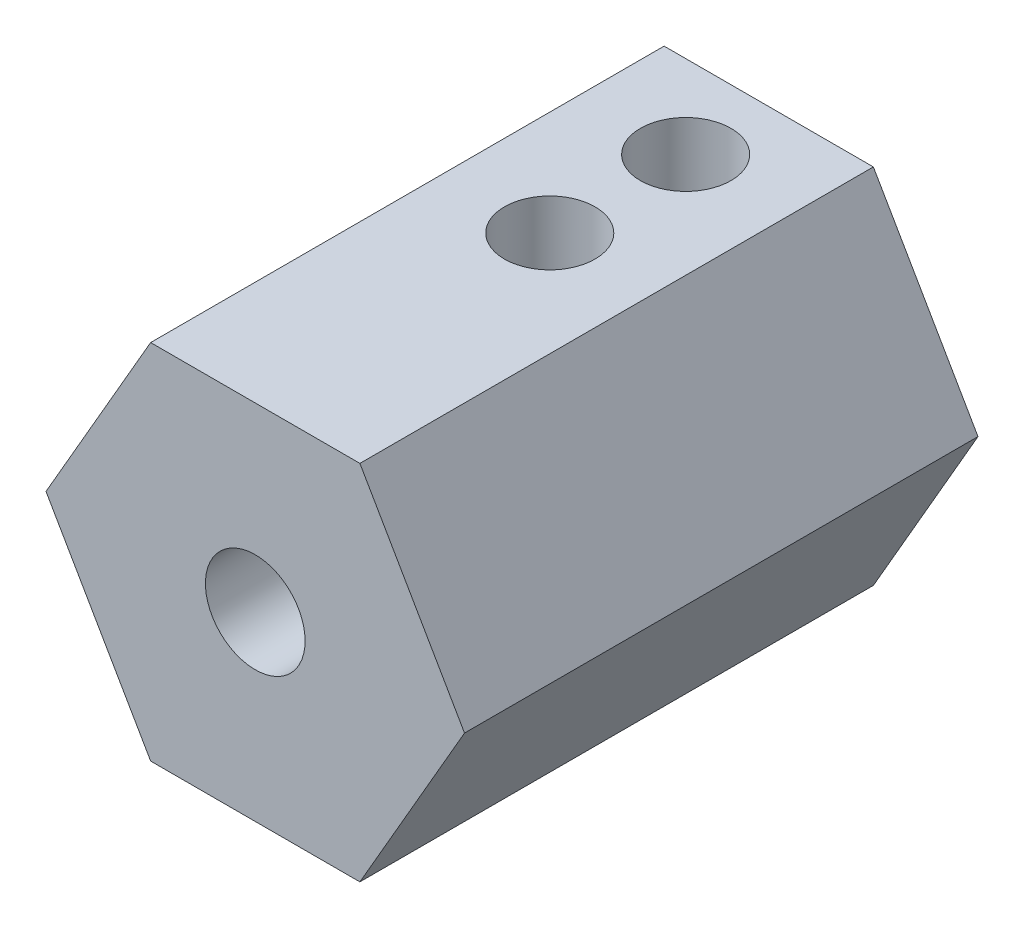
SolidWorks part; units mm, degrees
material "6061-T6 (SS)"
ref_plane "Front Plane" through (0, 0, 0) normal (0, 0, 1) x (1, 0, 0)
ref_plane "Top Plane" through (0, 0, 0) normal (0, 1, 0) x (1, 0, 0)
ref_plane "Right Plane" through (0, 0, 0) normal (1, 0, 0) x (0, 0, -1)
sketch "Sketch1" plane through (0, 0, 0) normal (0, 0, 1) x (1, 0, 0)
  line L1 (3.4641, 6) -> (-3.4641, 6)
  line L2 (-3.4641, 6) -> (-6.9282, 0)
  line L3 (-6.9282, 0) -> (-3.4641, -6)
  line L4 (-3.4641, -6) -> (3.4641, -6)
  line L5 (3.4641, -6) -> (6.9282, 0)
  line L6 (6.9282, 0) -> (3.4641, 6)
  circle A0 centre (0, 0) radius 6 construction
  dimension "D1" = 12
extrude "Boss-Extrude1" add sketch "Sketch1" along normal mid plane 17
ref_plane "Plane1" through (0, 0, 1.5) normal (0, 0, 1) x (1, 0, 0)
sketch "Sketch2" plane through (0, 0, -8.5) normal (0, 0, -1) x (-1, 0, 0)
  circle A0 centre (0, 0) radius 2
  dimension "D1" = 4
extrude "Cut-Extrude1" cut sketch "Sketch2" against normal up to surface (10 mm away)
hole_wizard "M4x0.7 Tapped Hole1" positions "Sketch6" profile "Sketch8" tap size "M4x0.7" standard "ANSI Metric"
sketch "Sketch6" plane through (0, 0, 8.5) normal (0, 0, 1) x (1, 0, 0)
  point P0 (0, 0)
sketch "Sketch8" plane through (0, 0, 8.5) normal (1, 0, 0) x (0, -1, 0)
  line L0 (0, 0) -> (0, 7.9914)
  line L1 (0, 7.9914) -> (1.65, 7)
  line L2 (1.65, 7) -> (1.65, 0)
  line L5 (1.65, 0) -> (0, 0)
  line L10 (0, 7.9914) -> (-1.65, 7) construction
  line L11 (0, -6.35) -> (0, 107.95) construction
  dimension "Tap Drill Dia." = 3.3
  dimension "Tap Drill Depth" = 7
  dimension "Drill Angle" = 118
cosmetic thread "Hole Thread1" parameters "D1"=8, "D2"=4
hole_wizard "M3x0.5 Tapped Hole1" positions "Sketch4" profile "Sketch5" tap size "M3x0.5" standard "ANSI Metric"
sketch "Sketch4" plane through (0, 6, 0) normal (0, 1, 0) x (1, 0, 0)
  line L0 (0, 5.75) -> (0, 1.25) construction
  line L1 (3.4641, 8.5) -> (-3.4641, 8.5) construction
  point P1 (0, 5.75)
  point P2 (0, 1.25)
  dimension "D1" = 4.5
  dimension "D2" = 2.75
sketch "Sketch5" plane through (0, 6, -5.75) normal (1, 0, 0) x (0, 0, 1)
  line L0 (0, 0) -> (0, 4)
  line L1 (0, 4) -> (1.5, 4)
  line L2 (1.5, 4) -> (1.5, 0)
  line L5 (1.5, 0) -> (0, 0)
  line L11 (0, -6.35) -> (0, 107.95) construction
  dimension "Thread Major Dia." = 3
  dimension "Thru Tap Drill Depth" = 4
